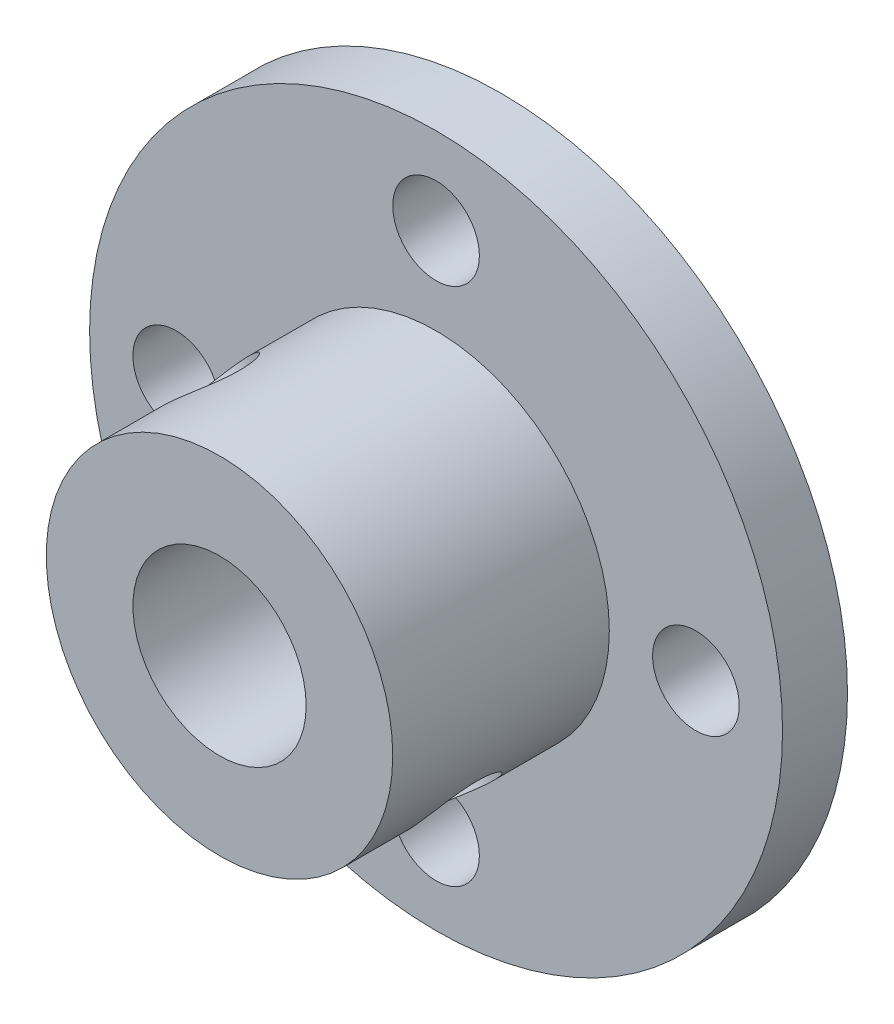
SolidWorks part; units mm, degrees
ref_plane "Спереди" through (0, 0, 0) normal (0, 0, 1) x (1, 0, 0)
ref_plane "Сверху" through (0, 0, 0) normal (0, 1, 0) x (1, 0, 0)
ref_plane "Справа" through (0, 0, 0) normal (1, 0, 0) x (0, 0, -1)
other "Configuration Table"
sketch "Sketch1" plane through (0, 0, 0) normal (0, 0, 1) x (1, 0, 0)
  circle A0 centre (0, 0) radius 16
  dimension "D1" = 32
extrude "Boss-Extrude1" add sketch "Sketch1" along normal blind 3
sketch "Sketch3" plane through (0, 0, 3) normal (0, 0, 1) x (1, 0, 0)
  circle A0 centre (0, 0) radius 8
  dimension "D1" = 16
extrude "Boss-Extrude2" add sketch "Sketch3" along normal blind 10
sketch "Sketch2" plane through (0, 0, 3) normal (0, 0, 1) x (1, 0, 0)
  line L0 (0, 12) -> (0, 0) construction
  circle A0 centre (0, 12) radius 2
  circle A1 centre (12, 0) radius 2
  circle A2 centre (0, -12) radius 2
  circle A3 centre (-12, 0) radius 2
  dimension "D1" = 4
  dimension "D3" = 24
  dimension "D2" = 4
extrude "Cut-Extrude1" cut sketch "Sketch2" against normal up to next
sketch "Sketch4" plane through (0, 0, 3) normal (0, 0, 1) x (1, 0, 0)
  line L0 (-11.3137, 11.3137) -> (0, 0) construction
  line L1 (0, 0) -> (0, 16.856) construction
  circle A0 centre (0, 0) radius 16 construction
  dimension "D1" = 45
ref_plane "Plane1" through (5.6569, -5.6569, 0) normal (0.7071, -0.7071, 0) x (-0.7071, -0.7071, 0)
sketch "Sketch5" plane through (5.6569, -5.6569, 0) normal (0.7071, -0.7071, 0) x (-0.7071, -0.7071, 0)
  line L0 (0, -3) -> (0, -13) construction
  line L3 (-8, -13) -> (8, -13) construction
  line L4 (0, -3) -> (-11.919, -3) construction
  circle A0 centre (0, -8) radius 2
  point P3 (0, 0)
  point P5 (0, -8)
  point P6 (0, 0)
  point P7 (0, -3)
  dimension "D1" = 4
extrude "Cut-Extrude2" cut sketch "Sketch5" against normal up to next
sketch "Sketch6" plane through (0, 0, 13) normal (0, 0, 1) x (1, 0, 0)
  circle A0 centre (0, 0) radius 4
  dimension "D1" = 8
extrude "Cut-Extrude3" cut sketch "Sketch6" against normal up to surface (13 mm away) up to face at (2, 12, 0)
